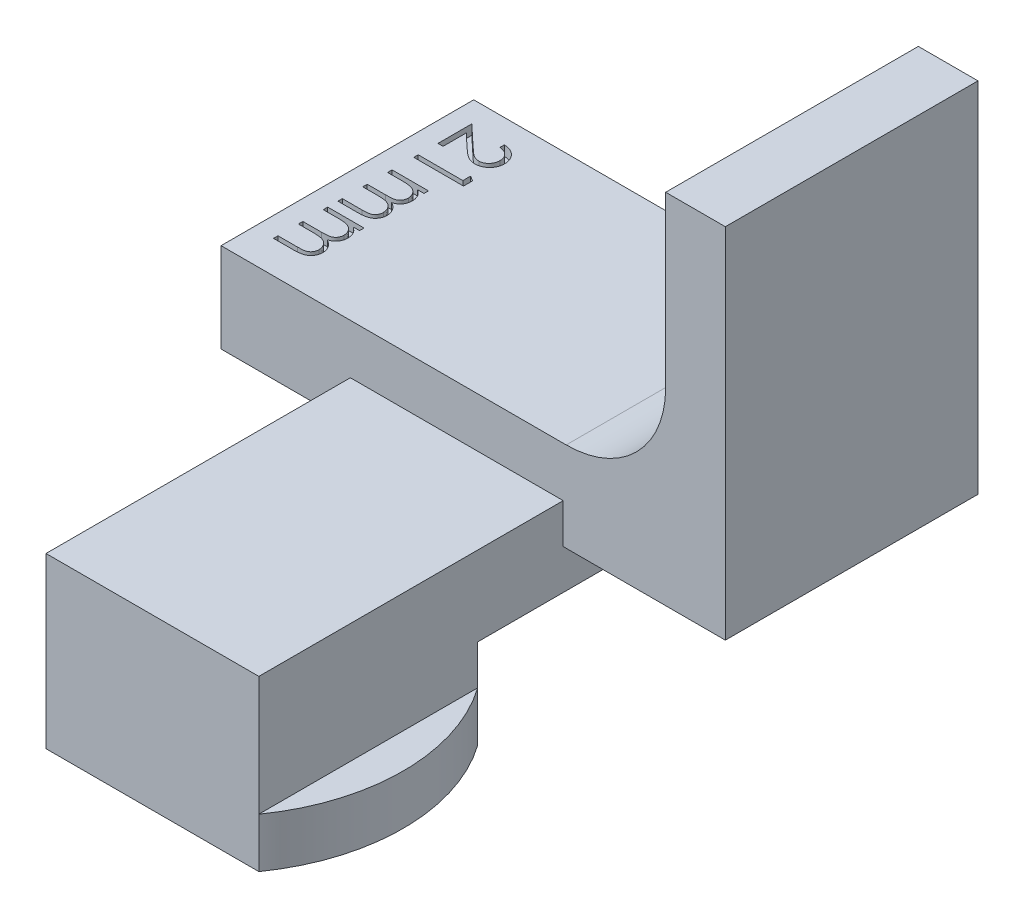
SolidWorks part; units mm, degrees
ref_plane "Front Plane" through (0, 0, 0) normal (0, 0, 1) x (1, 0, 0)
ref_plane "Top Plane" through (0, 0, 0) normal (0, 1, 0) x (1, 0, 0)
ref_plane "Right Plane" through (0, 0, 0) normal (1, 0, 0) x (0, 0, -1)
sketch "Sketch1" plane through (0, 0, 0) normal (0, 0, 1) x (1, 0, 0)
  line L0 (0, 0) -> (0, -4)
  line L1 (0, -4) -> (-1.75, -4)
  line L2 (-1.75, -4) -> (-1.75, -6.5)
  line L8 (12.45, -6.5) -> (12.45, -4)
  line L9 (12.45, -4) -> (10.7, -4)
  line L10 (10.7, -4) -> (10.7, 0)
  line L11 (10.7, 0) -> (18.85, 0)
  line L12 (18.85, 0) -> (18.85, 18)
  line L13 (18.85, 18) -> (15.85, 18)
  line L14 (15.85, 18) -> (15.85, 4.5)
  line L15 (15.85, 4.5) -> (-6.5, 4.5)
  line L16 (-6.5, 4.5) -> (-6.5, 0)
  line L17 (-6.5, 0) -> (0, 0)
  line L18 (5.35, -6.5) -> (5.35, 15) construction
  line L19 (-1.75, -6.5) -> (12.45, -6.5)
  circle A0 centre (5.35, 15) radius 10.5 construction
  point P3 (5.35, -6.5)
  dimension "D9" = 15
  dimension "D8" = 21
  dimension "D2" = 2.5
  dimension "D3" = 10.7
  dimension "D4" = 4
  dimension "D5" = 14.2
  dimension "D6" = 3
  dimension "D7" = 3
  dimension "D10" = 6.5
extrude "Boss-Extrude1" add sketch "Sketch1" along normal blind 12.7
fillet "Fillet1" radius 5 1 edges at (15.85, 4.5, 6.35)
sketch "Sketch3" plane through (0, 0, 12.7) normal (0, 0, 1) x (1, 0, 0)
  line L0 (0, 0) -> (0, 2)
  line L1 (0, 2) -> (10.7, 2)
  line L2 (10.7, 2) -> (10.7, 0)
  line L14 (-6.5, 0) -> (0, 0)
  line L15 (0, 0) -> (0, -4)
  line L16 (0, -4) -> (-1.75, -4)
  line L17 (-1.75, -4) -> (-1.75, -6.5)
  line L18 (-1.75, -6.5) -> (12.45, -6.5)
  line L19 (12.45, -6.5) -> (12.45, -4)
  line L20 (12.45, -4) -> (10.7, -4)
  line L21 (10.7, -4) -> (10.7, 0)
  line L22 (10.7, 0) -> (18.85, 0)
  line L23 (18.85, 0) -> (18.85, 18)
  line L24 (18.85, 18) -> (15.85, 18)
  line L25 (15.85, 18) -> (15.85, 9.5)
  line L26 (10.85, 4.5) -> (-6.5, 4.5)
  line L27 (-6.5, 4.5) -> (-6.5, 0)
  line L29 (0, 0) -> (0, -4)
  line L30 (0, -4) -> (-1.75, -4)
  line L31 (-1.75, -4) -> (-1.75, -6.5)
  line L32 (-1.75, -6.5) -> (12.45, -6.5)
  line L33 (12.45, -6.5) -> (12.45, -4)
  line L34 (12.45, -4) -> (10.7, -4)
  line L35 (10.7, -4) -> (10.7, 0)
  arc A1 (10.85, 4.5) -> (15.85, 9.5) centre (10.85, 9.5) ccw
  dimension "D2" = 2
  dimension "D1" = 0
extrude "Boss-Extrude2" add sketch "Sketch3" along normal blind 28 from surface at -12.7 starting at face at (7.4057, 1.631, 0)
sketch "Sketch4" plane through (0, 0, 0) normal (0, 0, -1) x (-1, 0, 0)
  line L0 (6.5, 0) -> (0, 0) construction
  line L1 (-12.45, -6.5) -> (1.75, -6.5)
  line L2 (-12.45, -6.5) -> (-12.45, -2)
  line L3 (-12.45, -2) -> (1.75, -2)
  line L4 (1.75, -6.5) -> (1.75, -2)
  dimension "D1" = 2
extrude "Cut-Extrude2" cut sketch "Sketch4" against normal blind 17
sketch "Sketch2" plane through (0, -4, 0) normal (0, 1, 0) x (1, 0, 0)
  line L0 (0, -28) -> (10.7, -28)
  line L1 (10.7, -17) -> (0, -17)
  line L6 (12.45, -28) -> (12.45, -17) construction
  line L7 (-1.75, -28) -> (-1.75, -17) construction
  arc A4 (0, -17) -> (0, -28) centre (7.7679, -22.5) ccw
  arc A6 (10.7, -28) -> (10.7, -17) centre (2.9321, -22.5) ccw
extrude "Cut-Extrude1" cut sketch "Sketch2" against normal blind 10 flip side to cut
sketch "Sketch5" plane through (0, 4.5, 0) normal (0, 1, 0) x (1, 0, 0)
  line L0 (-5.5, -1) -> (-5.5, -10.9086) construction
  line L1 (-6.5, -12.7) -> (-6.5, 0) construction
  line L2 (10.85, 0) -> (-6.5, 0) construction
  text T0 "21mm" font "Century Gothic" height 2.5
  dimension "D1" = 1
  dimension "D2" = 1
extrude "Cut-Extrude3" cut sketch "Sketch5" against normal blind 0.5
